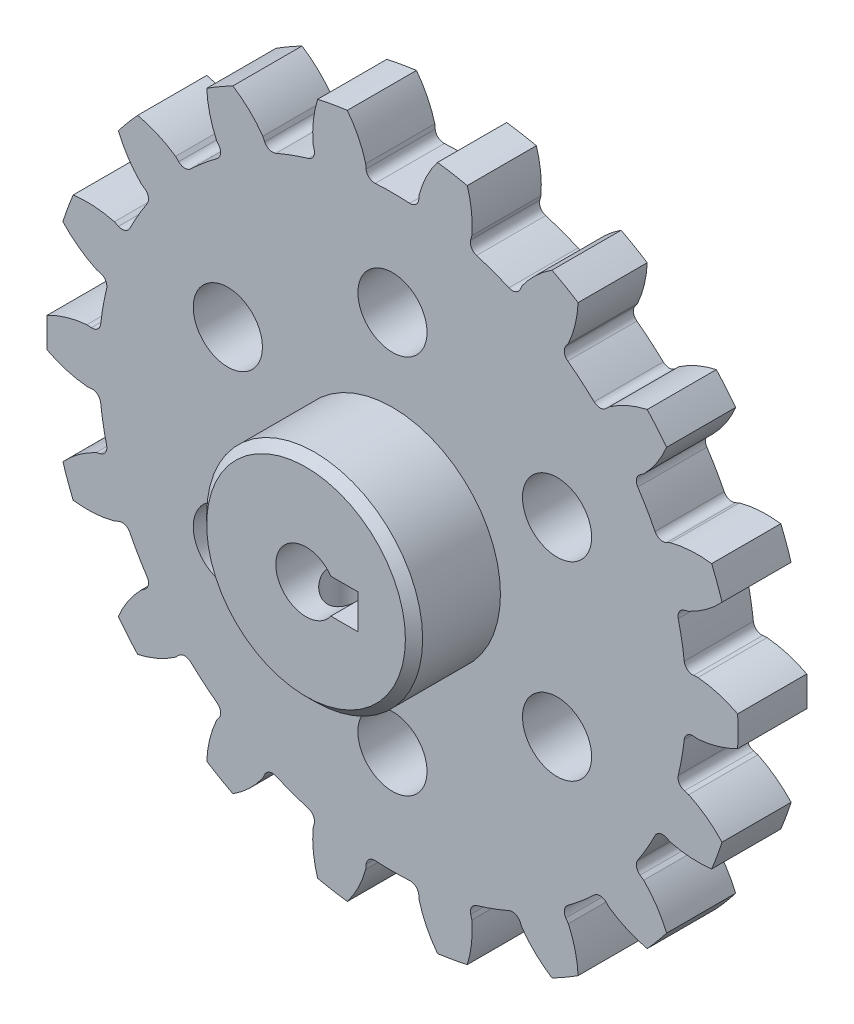
SolidWorks part; units mm, degrees
ref_plane "Plan de face" through (0, 0, 0) normal (0, 0, 1) x (1, 0, 0)
ref_plane "Plan de dessus" through (0, 0, 0) normal (0, 1, 0) x (1, 0, 0)
ref_plane "Plan de droite" through (0, 0, 0) normal (1, 0, 0) x (0, 0, -1)
sketch "Esquisse1" plane through (0, 0, 0) normal (0, 0, 1) x (1, 0, 0)
  line L0 (0, 0) -> (49.1646, 0) construction
  line L1 (0, 0) -> (33.4835, 5.904) construction
  line L2 (0, 0) -> (40.5362, 3.5465) construction
  line L3 (0, 0) -> (40.5296, 1.7696) construction
  line L4 (33.8706, -2.9633) -> (35.3649, -3.094)
  line L5 (0, 0) -> (33.4835, 5.904)
  line L6 (33.8706, 2.9633) -> (35.3649, 3.094)
  line L7 (0, 0) -> (33.4835, -5.904)
  circle A0 centre (0, 0) radius 40 construction
  circle A1 centre (0, 0) radius 35.5 construction
  circle A2 centre (0, 0) radius 34 construction
  arc A3 (33.4835, 5.904) -> (33.8706, 2.9633) centre (0, 0) cw
  arc A4 (39.9546, -1.7445) -> (39.9546, 1.7445) centre (0, 0) ccw
  arc A5 (35.3649, 3.094) -> (39.9546, 1.7445) centre (34.1869, -9.3916) cw
  arc A6 (35.3649, -3.094) -> (39.9546, -1.7445) centre (34.1869, 9.3916) ccw
  arc A7 (33.4835, -5.904) -> (33.8706, -2.9633) centre (0, 0) ccw
  dimension "D1" = 80
  dimension "D2" = 71
  dimension "D3" = 6
  dimension "D4" = 10
  dimension "D5" = 5
  dimension "D6" = 2.5
extrude "Boss.-Extru.1" add sketch "Esquisse1" along normal blind 8 contours L7 A7 L4 A6 A4 A5 L6 A3 L5
fillet "Congé1" radius 1 2 edges at (33.8706, -2.9633, 4) (33.8706, 2.9633, 4)
pattern_circular "Répétition circulaire2" count 18 over 360 about axis through (0, 0, 0) along (0, 0, 1) of "Congé1", "Boss.-Extru.1"
sketch "Esquisse3" plane through (0, 0, 8) normal (0, 0, 1) x (1, 0, 0)
  circle A0 centre (0, 0) radius 12.5
  dimension "D1" = 25
extrude "Boss.-Extru.2" add sketch "Esquisse3" along normal blind 10
sketch "Esquisse5" plane through (0, 0, 18) normal (0, 0, 1) x (1, 0, 0)
  circle A0 centre (0, 0) radius 3.5
  dimension "D1" = 7
sketch "Esquisse7" plane through (0, 0, 18) normal (0, 0, 1) x (1, 0, 0)
  line L1 (0, 2) -> (6, 2)
  line L2 (0, 2) -> (0, -2)
  line L3 (0, -2) -> (6, -2)
  line L4 (6, 2) -> (6, -2)
  dimension "D1" = 2
  dimension "D2" = 2
  dimension "D3" = 6
extrude "Enlèv. mat.-Extru.2" cut sketch "Esquisse7" against normal up to surface (10 mm away) contours L1 L4 L3 L2 up to face at (-12.5, 0, 8)
extrude "Enlèv. mat.-Extru.3" cut sketch "Esquisse5" against normal up to surface (18 mm away) up to face at (0, 0, 0)
sketch "Esquisse8" plane through (0, 0, 0) normal (0, 1, 0) x (1, 0, 0)
  line L0 (-12.5, -18) -> (12.5, -18) construction
  circle A0 centre (0, -13) radius 2.5
  dimension "D1" = 5
  dimension "D2" = 5
extrude "Enlèv. mat.-Extru.4" cut sketch "Esquisse8" against normal up to surface (12.5 mm away) contours A0
chamfer "Chanfrein1" distance 1 angle 45 1 edges at (12.5, 0, 18)
sketch "Esquisse9" plane through (0, 0, 8) normal (0, 0, 1) x (1, 0, 0)
  circle A0 centre (0, 22) radius 4
  dimension "D1" = 8
  dimension "D2" = 22
extrude "Enlèv. mat.-Extru.5" cut sketch "Esquisse9" against normal up to surface (8 mm away) up to face at (-3.5, 0, 0)
pattern_circular "Répétition circulaire3" count 6 over 360 about axis through (0, 0, 0) along (0, 0, 1) of "Enlèv. mat.-Extru.5"
